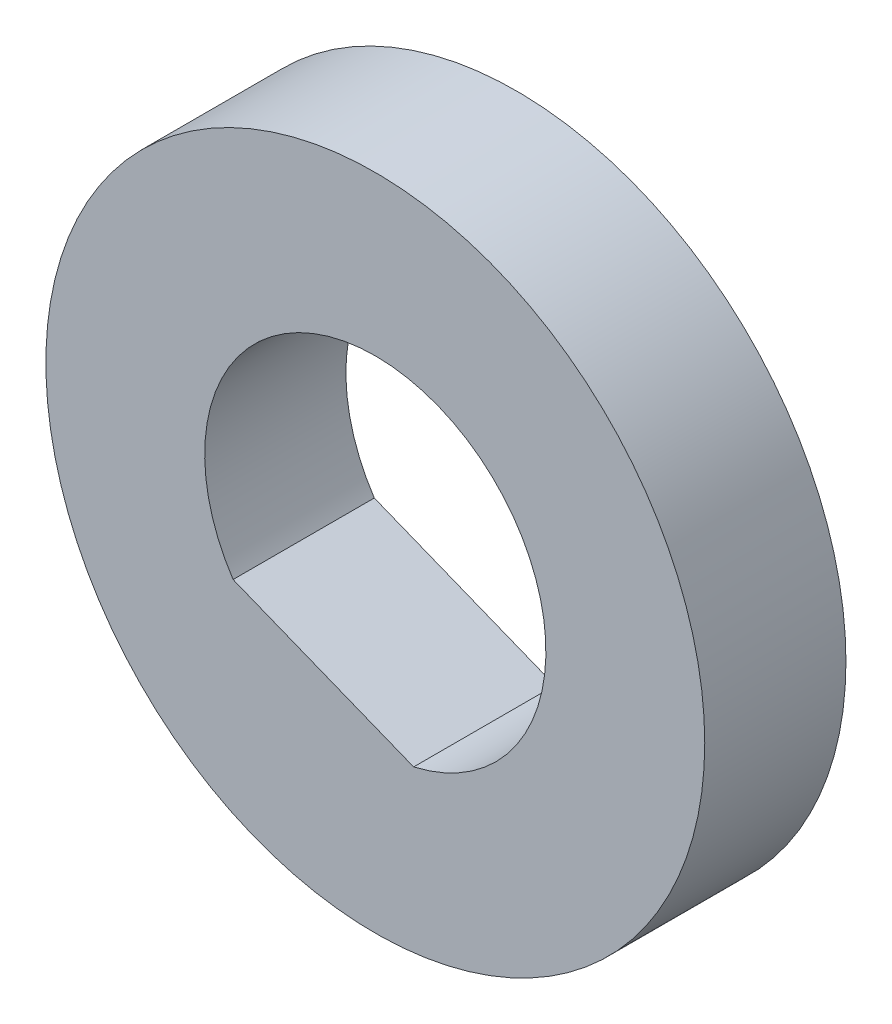
SolidWorks part; units mm, degrees
ref_plane "Plan de face" through (0, 0, 0) normal (0, 0, 1) x (1, 0, 0)
ref_plane "Plan de dessus" through (0, 0, 0) normal (0, 1, 0) x (1, 0, 0)
ref_plane "Plan de droite" through (0, 0, 0) normal (1, 0, 0) x (0, 0, -1)
sketch "Esquisse1" plane through (0, 0, 0) normal (0, 0, 1) x (1, 0, 0)
  circle A0 centre (0, 0) radius 14
  dimension "D1" = 28
extrude "Boss.-Extru.1" add sketch "Esquisse1" along normal blind 6 contours A0
sketch "Esquisse2" plane through (0, 0, 0) normal (0, 0, 1) x (1, 0, 0)
  line L1 (1.6286, -7.0647) -> (-6.0436, -4.0046)
  circle A1 centre (0, 0) radius 7.25 construction
  arc A2 (-6.0436, -4.0046) -> (1.6286, -7.0647) centre (0, 0) cw
  dimension "D2" = 7.25
  dimension "D1" = 8.26
extrude "Enlèv. mat.-Extru.1" cut sketch "Esquisse2" along normal blind 16
